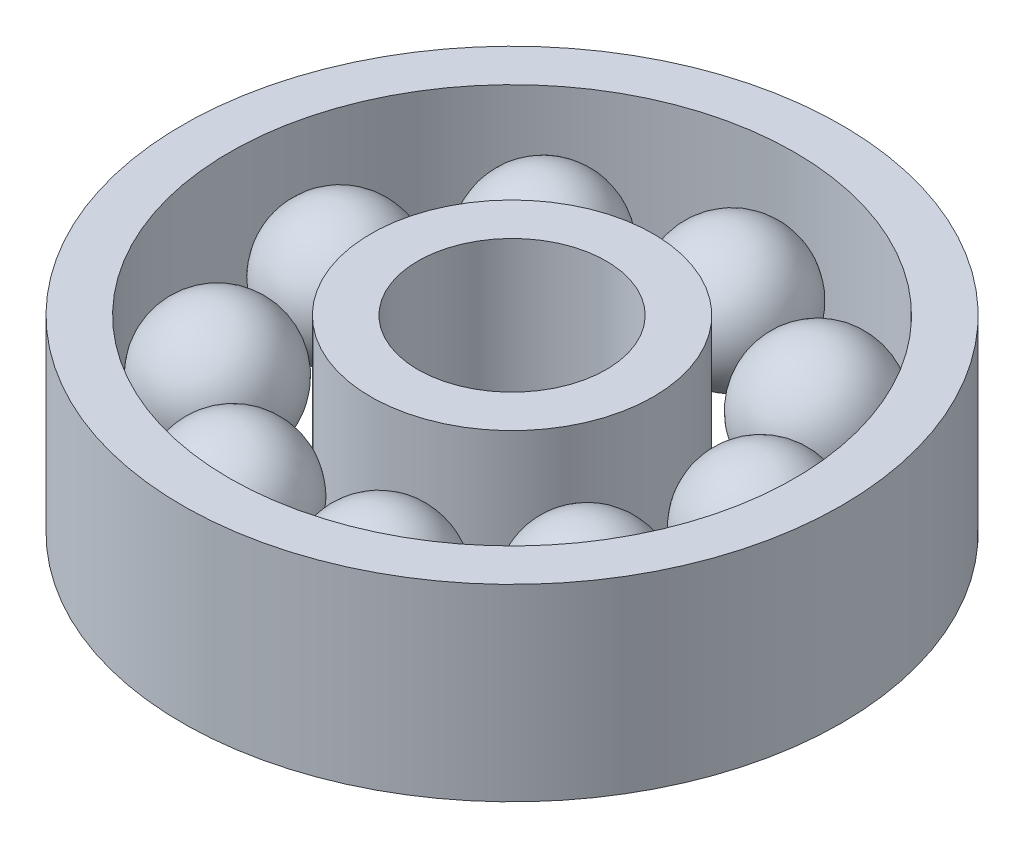
SolidWorks part; units mm, degrees
ref_plane "Front Plane" through (0, 0, 0) normal (0, 0, 1) x (1, 0, 0)
ref_plane "Top Plane" through (0, 0, 0) normal (0, 1, 0) x (1, 0, 0)
ref_plane "Right Plane" through (0, 0, 0) normal (1, 0, 0) x (0, 0, -1)
sketch "Sketch1" plane through (0, 0, 0) normal (0, 1, 0) x (1, 0, 0)
  circle A0 centre (0, 0) radius 4
  circle A1 centre (0, 0) radius 12
extrude "Extrude-Thin1" add sketch "Sketch1" along normal mid plane 8 thin
sketch "Sketch2" plane through (0, 0, 0) normal (0, 1, 0) x (1, 0, 0)
  line L0 (0.0895, 11.9997) -> (0.1683, 6.4002) construction
  line L1 (0.0895, 11.9997) -> (0.1683, 6.4002)
  arc A0 (0.0895, 11.9997) -> (0.1683, 6.4002) centre (0.1289, 9.1999) cw
  circle A1 centre (0, 0) radius 12 construction
  circle A2 centre (0, 0) radius 14 construction
  point P5 (1.0944, 9.1999)
  point P6 (1.7614, 11.87)
  point P7 (-1.0407, 6.5081)
  dimension "D1" = 2.8
  dimension "D3" = 9.1999
revolve "Revolve1" add sketch "Sketch2" angle 360 about L0
pattern_circular "CirPattern1" count 9 over 360 about axis through (0, 0, 0) along (0, 1, 0) of "Revolve1"
